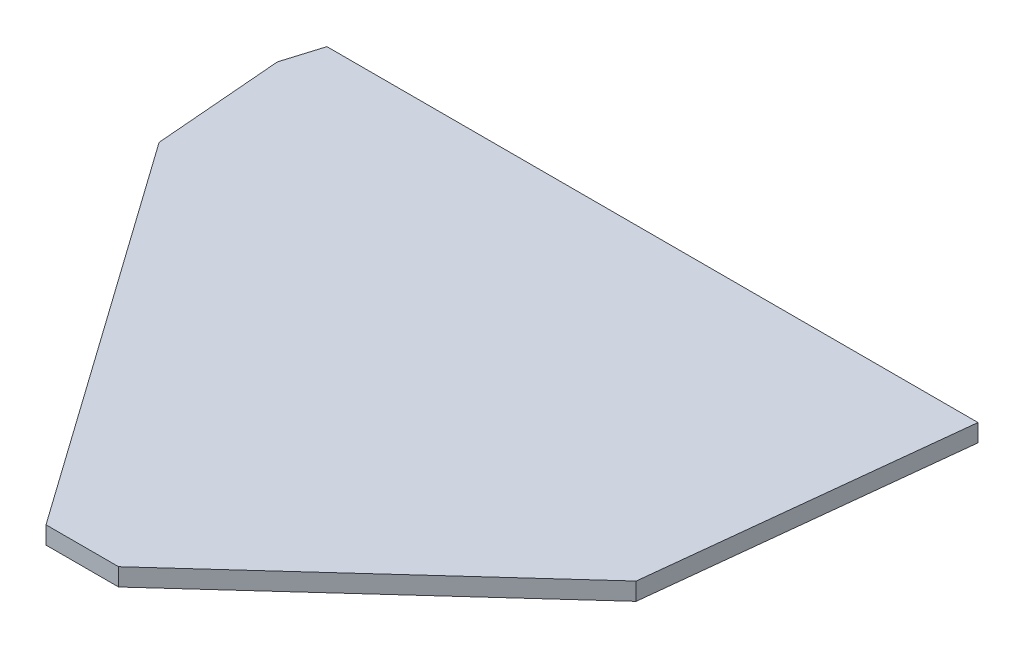
SolidWorks part; units mm, degrees
ref_plane "Plan de face" through (0, 0, 0) normal (0, 0, 1) x (1, 0, 0)
ref_plane "Plan de dessus" through (0, 0, 0) normal (0, 1, 0) x (1, 0, 0)
ref_plane "Plan de droite" through (0, 0, 0) normal (1, 0, 0) x (0, 0, -1)
sketch "Esquisse1" plane through (0, 0, 0) normal (0, 1, 0) x (1, 0, 0)
  line L0 (39.0812, 28.0047) -> (42.9063, 63.0412)
  line L1 (42.9063, 63.0412) -> (-31.1056, 63.0412)
  line L2 (-31.1056, 63.0412) -> (-32.4216, 58.7227)
  line L3 (-32.4216, 58.7227) -> (-31.2216, 44.0782)
  line L4 (-31.2216, 44.0782) -> (0, 0)
  line L5 (0, 0) -> (8.2473, 0)
  line L6 (8.2473, 0) -> (39.0812, 28.0047)
  point P7 (0, 0)
  point P8 (0, 0)
  point P9 (0, 0)
extrude "Boss.-Extru.1" add sketch "Esquisse1" along normal blind 2
